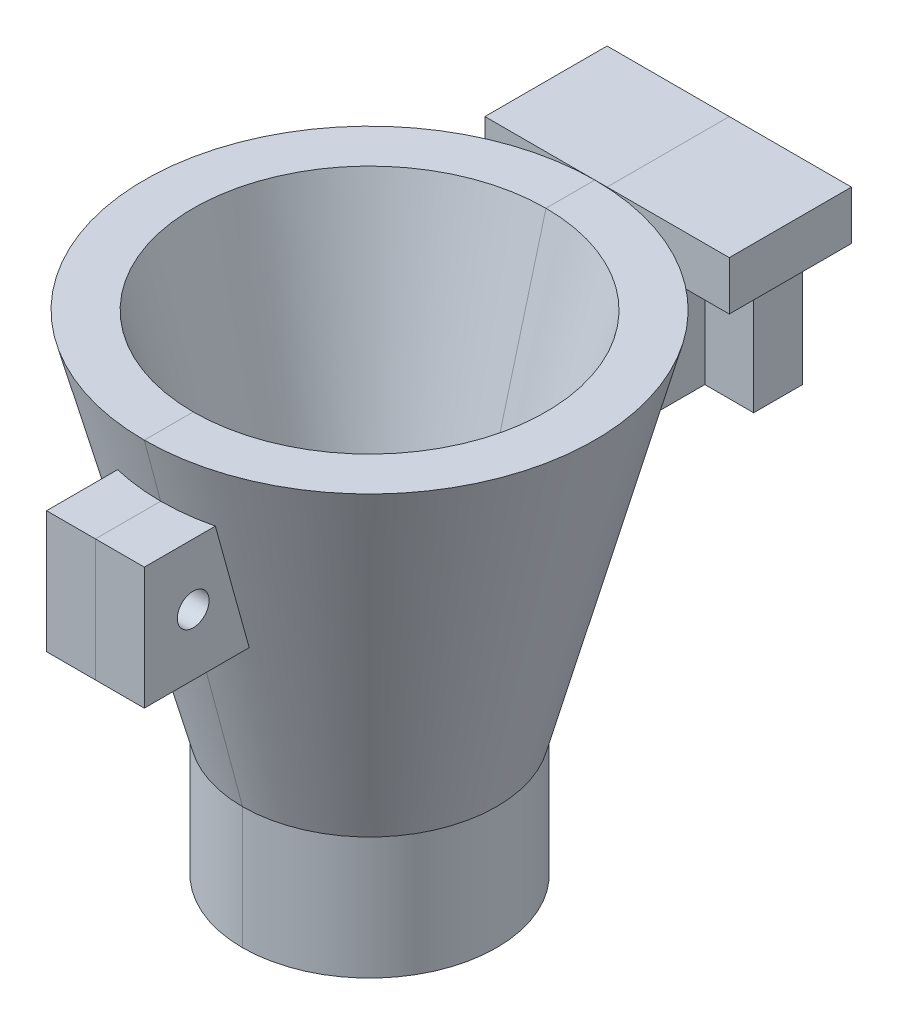
SolidWorks part; units mm, degrees
ref_plane "Front Plane" through (0, 0, 0) normal (0, 0, 1) x (1, 0, 0)
ref_plane "Top Plane" through (0, 0, 0) normal (0, 1, 0) x (1, 0, 0)
ref_plane "Right Plane" through (0, 0, 0) normal (1, 0, 0) x (0, 0, -1)
sketch "Sketch1" plane through (0, 0, 0) normal (0, 0, 1) x (1, 0, 0)
  line L0 (8.128, -12.7) -> (18.3369, 25.4)
  line L1 (8.128, -12.7) -> (13.208, -12.7)
  line L2 (18.3369, 25.4) -> (23.4169, 25.4)
  line L3 (13.208, -12.7) -> (23.4169, 25.4)
  line L4 (0, 0) -> (0, 10.8986) construction
  line L6 (13.208, -12.7) -> (8.128, -12.7)
  line L7 (13.208, -12.7) -> (13.208, -25.4)
  line L8 (13.208, -25.4) -> (8.128, -25.4)
  line L9 (8.128, -12.7) -> (8.128, -25.4)
  dimension "D1" = 105
  dimension "D2" = 12.7
  dimension "D3" = 5.08
  dimension "D4" = 38.1
  dimension "D5" = 8.128
  dimension "D6" = 12.7
revolve "Revolve1" add sketch "Sketch1" angle 360 about L4
sketch "Sketch13" plane through (0, 0, 0) normal (1, 0, 0) x (0, 0, -1)
  line L0 (23.4169, 25.4) -> (-23.4169, 25.4) construction
  line L1 (0.1456, 19.05) -> (-34.8469, 19.05)
  line L2 (0.1456, 19.05) -> (0.1456, 6.35)
  line L3 (0.1456, 6.35) -> (-34.8469, 6.35)
  line L4 (-34.8469, 19.05) -> (-34.8469, 6.35)
  circle A0 centre (-23.4169, 12.7) radius 1.651
  point P9 (-34.8469, 12.7)
  dimension "D4" = 3.302
  dimension "D1" = 6.35
  dimension "D2" = 12.7
  dimension "D3" = 11.43
extrude "Boss-Extrude1" add sketch "Sketch13" along normal mid plane 10.16 contours L2 L1 L4 L3
mirror "Mirror1" about plane through (0, 0, 0) normal (0, 0, 1) of "Boss-Extrude1"
sketch "Sketch14" plane through (0, 19.05, 0) normal (0, 1, 0) x (1, 0, 0)
  line L0 (5.08, 34.8469) -> (-5.08, 34.8469) construction
  line L1 (-10.16, 29.7669) -> (10.16, 29.7669)
  line L2 (-10.16, 29.7669) -> (-10.16, 34.8469)
  line L3 (-10.16, 34.8469) -> (10.16, 34.8469)
  line L4 (10.16, 29.7669) -> (10.16, 34.8469)
  line L5 (-10.16, 29.7669) -> (10.16, 34.8469) construction
  line L6 (-10.16, 34.8469) -> (10.16, 29.7669) construction
  line L7 (5.08, 21.1128) -> (5.08, 34.8469) construction
  point P0 (0, 32.3069)
  dimension "D1" = 5.08
  dimension "D2" = 5.08
extrude "Boss-Extrude2" add sketch "Sketch14" against normal up to surface (12.7 mm away) up to face at (0, 6.35, -26.4)
sketch "Sketch15" plane through (0, 19.05, 0) normal (0, 1, 0) x (1, 0, 0)
  line L1 (7.62, 27.2269) -> (12.7, 27.2269)
  line L2 (12.7, 27.2269) -> (12.7, 37.3869)
  line L3 (12.7, 37.3869) -> (-12.7, 37.3869)
  line L4 (-12.7, 37.3869) -> (-12.7, 27.2269)
  line L5 (-12.7, 27.2269) -> (-7.62, 27.2269)
  line L7 (5.08, 21.1128) -> (5.08, 29.7669)
  line L8 (5.08, 29.7669) -> (10.16, 29.7669)
  line L9 (10.16, 29.7669) -> (10.16, 34.8469)
  line L10 (10.16, 34.8469) -> (-10.16, 34.8469)
  line L11 (-10.16, 34.8469) -> (-10.16, 29.7669)
  line L12 (-10.16, 29.7669) -> (-5.08, 29.7669)
  line L13 (-5.08, 29.7669) -> (-5.08, 21.1128)
  line L14 (5.08, 27.2269) -> (5.08, 29.7669)
  line L15 (5.08, 29.7669) -> (10.16, 29.7669)
  line L16 (10.16, 29.7669) -> (10.16, 34.8469)
  line L17 (10.16, 34.8469) -> (-10.16, 34.8469)
  line L18 (-10.16, 34.8469) -> (-10.16, 29.7669)
  line L19 (-10.16, 29.7669) -> (-5.08, 29.7669)
  line L20 (-5.08, 29.7669) -> (-5.08, 27.2269)
  line L21 (-7.62, 27.2269) -> (7.62, 27.2269)
  line L22 (-5.08, 29.7669) -> (-5.08, 21.1128) construction
  line L23 (-7.62, 27.2269) -> (-7.62, 17.5963) construction
  line L24 (5.08, 21.1128) -> (5.08, 29.7669) construction
  line L25 (7.62, 17.5963) -> (7.62, 27.2269) construction
  line L27 (-12.7, 27.2269) -> (12.7, 27.2269)
  line L28 (-12.7, 27.2269) -> (-12.7, 24.6869)
  line L29 (-12.7, 24.6869) -> (12.7, 24.6869)
  line L30 (12.7, 27.2269) -> (12.7, 24.6869)
  arc A1 (5.08, 21.1128) -> (-5.08, 21.1128) centre (0, 0) ccw
  arc A3 (7.62, 17.5963) -> (-7.62, 17.5963) centre (0, 0) ccw construction
  arc A4 (5.08, 21.1128) -> (-5.08, 21.1128) centre (0, 0) ccw construction
  line M18 (5.08, 21.1128) -> (5.08, 29.7669)
  line M19 (5.08, 29.7669) -> (10.16, 29.7669)
  line M20 (10.16, 29.7669) -> (10.16, 34.8469)
  line M21 (10.16, 34.8469) -> (-10.16, 34.8469)
  line M22 (-10.16, 34.8469) -> (-10.16, 29.7669)
  line M23 (-10.16, 29.7669) -> (-5.08, 29.7669)
  line M24 (-5.08, 29.7669) -> (-5.08, 21.1128)
  dimension "D3" = 2.54
  dimension "D1" = 0
  dimension "D2" = 2.54
extrude "Boss-Extrude3" add sketch "Sketch15" along normal blind 5.08 contours L5 L21 L1 L2 L3 L4 M24 M23 M22 M21 M20 M19 M18 | L21 M24 M18 M19 M20 M21 M22 M23 | L28 L27 L30 L29
sketch "Sketch16" plane through (5.08, 0, 0) normal (1, 0, 0) x (0, 0, -1)
  line L5 (-34.8469, 6.35) -> (-17.5937, 6.35) construction
  line L6 (-34.8469, 19.05) -> (-28.4969, 19.05)
  line L7 (-34.8469, 19.05) -> (-34.8469, 6.35)
  line L8 (-34.8469, 6.35) -> (-28.4969, 6.35)
  line L9 (-28.4969, 19.05) -> (-28.4969, 6.35)
  circle A1 centre (-23.4169, 12.7) radius 1.651 construction
  dimension "D1" = 5.08
extrude "Cut-Extrude6" cut sketch "Sketch16" against normal through all
sketch "Sketch17" plane through (0, 0, 0) normal (1, 0, 0) x (0, 0, -1)
  line L1 (8.128, -12.7) -> (-8.128, -12.7) construction
  line L2 (-18.3369, 25.4) -> (0, 25.4)
  line L6 (0, -12.7) -> (-8.128, -12.7)
  line L8 (0, 25.4) -> (0, -12.7)
  line L11 (-18.3369, 25.4) -> (-8.128, -12.7)
  line L18 (0, 25.4) -> (0, 31.5029) construction
revolve "Cut-Revolve1" cut sketch "Sketch17" angle 360 about L18
split "Split1" trim tools "Right Plane" bodies to split 124 resulting bodies 125 126
